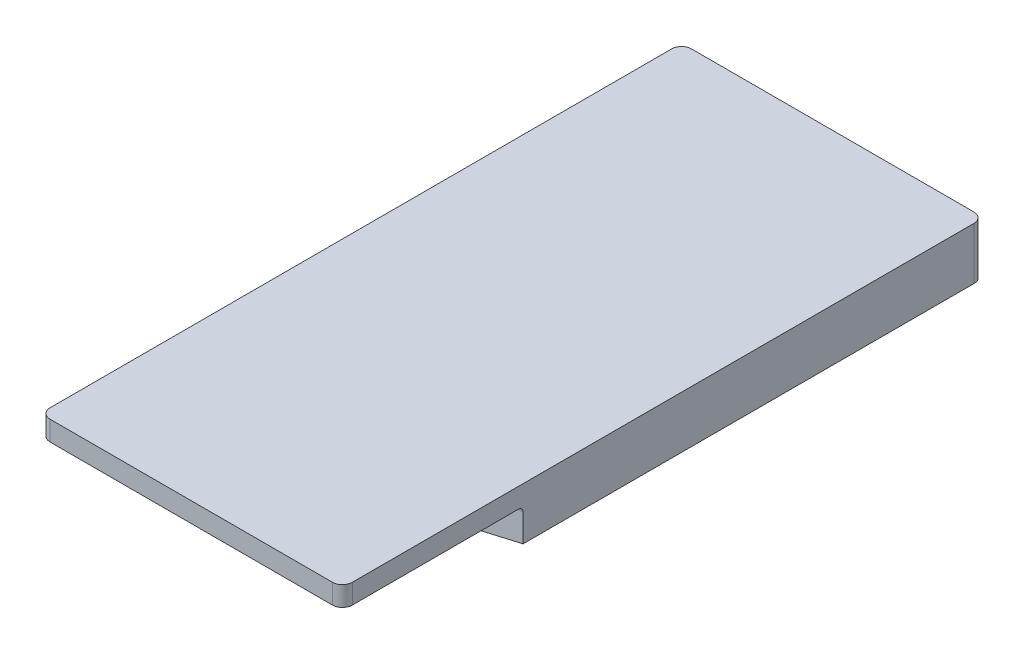
SolidWorks part; units mm, degrees
ref_plane "Front Plane" through (0, 0, 0) normal (0, 0, 1) x (1, 0, 0)
ref_plane "Top Plane" through (0, 0, 0) normal (0, 1, 0) x (1, 0, 0)
ref_plane "Right Plane" through (0, 0, 0) normal (1, 0, 0) x (0, 0, -1)
ref_plane "Plane1" through (0, 0, -411.75) normal (0, 0, -1) x (-1, 0, 0)
sketch "Sketch1" plane through (0, 0, -411.75) normal (0, 0, -1) x (-1, 0, 0)
  line L0 (121.01, 20.0097) -> (194.0105, 36.9542)
  line L1 (194.0105, 36.9542) -> (194.0105, 103.9042)
  line L2 (194.0105, 103.9042) -> (-194.0105, 103.9042)
  line L3 (-194.0105, 103.9042) -> (-194.0105, 36.9542)
  line L4 (-194.0105, 36.9542) -> (-121.01, 20.0097)
  line L5 (-121.01, 20.0097) -> (-121.01, 39)
  line L6 (-56.01, 39) -> (-56.01, 5.2065)
  line L7 (56.01, 5.2065) -> (56.01, 39)
  line L8 (121.01, 39) -> (121.01, 20.0097)
  arc A0 (-121.01, 39) -> (-56.01, 39) centre (-88.51, 39) cw
  arc A1 (-56.01, 5.2065) -> (56.01, 5.2065) centre (0, 303.8744) ccw
  arc A2 (56.01, 39) -> (121.01, 39) centre (88.51, 39) cw
extrude "Boss-Extrude1" add sketch "Sketch1" against normal blind 591.5
sketch "Sketch2" plane through (0, 0, 179.75) normal (0, 0, 1) x (1, 0, 0)
  line L0 (194.0105, 78.5) -> (-194.0105, 78.5)
  line L1 (-194.0105, 78.5) -> (-194.0105, 103.9042)
  line L2 (-194.0105, 103.9042) -> (194.0105, 103.9042)
  line L3 (194.0105, 103.9042) -> (194.0105, 78.5)
extrude "Boss-Extrude2" add sketch "Sketch2" along normal blind 232
fillet "Fillet1" radius 12.7 4 edges at (-194.0105, 91.2021, 411.75) (194.0105, 91.2021, 411.75) (194.0105, 70.4292, -411.75) (-194.0105, 70.4292, -411.75)
fillet "Fillet3" radius 6.35 1 edges at (0, 78.5, 179.75)
